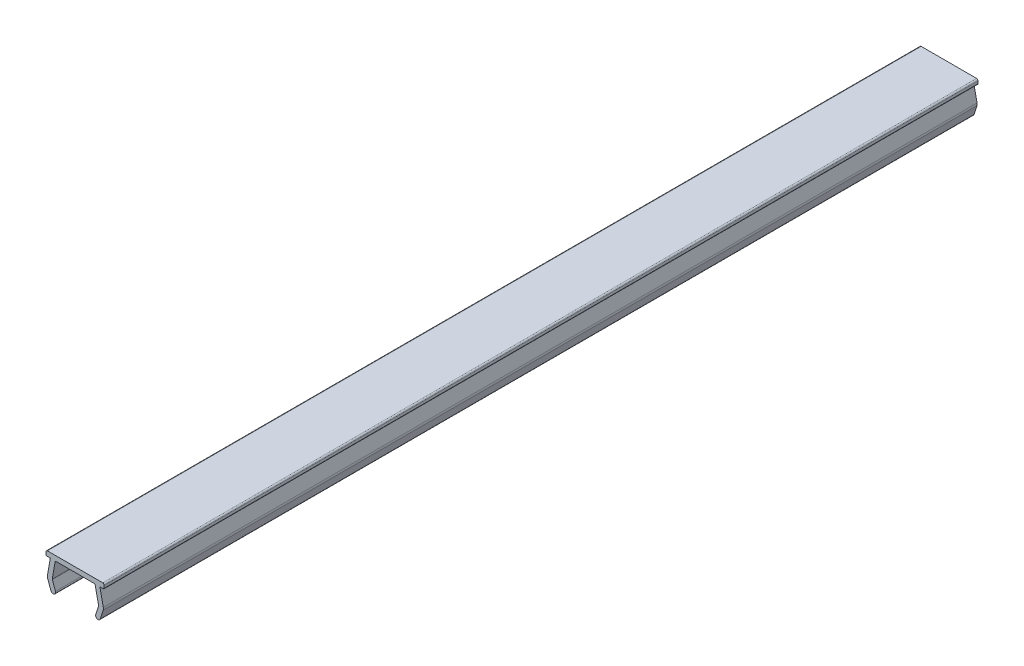
SolidWorks part; units mm, degrees
ref_plane "前视基准面" through (0, 0, 0) normal (0, 0, 1) x (1, 0, 0)
ref_plane "上视基准面" through (0, 0, 0) normal (0, 1, 0) x (1, 0, 0)
ref_plane "右视基准面" through (0, 0, 0) normal (1, 0, 0) x (0, 0, -1)
sketch "草图1" plane through (0, 0, 0) normal (0, 0, 1) x (1, 0, 0)
  line L1 (11.7861, 93.4475) -> (11.1854, 91.5991)
  line L2 (11.107, 97.2884) -> (11.8132, 93.9645)
  line L3 (11.8, 97.2884) -> (11.107, 97.2884)
  line L4 (12, 97.9884) -> (12, 97.4884)
  line L5 (0.3, 98.2884) -> (11.7, 98.2884)
  line L6 (0, 97.4884) -> (0, 97.9884)
  line L7 (0.893, 97.2884) -> (0.2, 97.2884)
  line L8 (0.2946, 93.8947) -> (0.893, 97.2884)
  line L9 (1.0076, 91.5441) -> (0.3398, 93.379)
  line L10 (1.3024, 93.6581) -> (1.9473, 91.8862)
  line L11 (1.8793, 97.1231) -> (1.2911, 93.787)
  line L12 (9.9273, 97.2884) -> (2.0763, 97.2884)
  line L13 (10.8239, 93.8308) -> (10.1229, 97.1299)
  line L14 (10.2343, 91.9082) -> (10.8172, 93.7015)
  arc A0 (11.7861, 93.4475) -> (11.8132, 93.9645) centre (10.8351, 93.7566) ccw
  arc A1 (11.8, 97.2884) -> (12, 97.4884) centre (11.8, 97.4884) ccw
  arc A2 (12, 97.9884) -> (11.7, 98.2884) centre (11.7, 97.9884) ccw
  arc A3 (0.3, 98.2884) -> (0, 97.9884) centre (0.3, 97.9884) ccw
  arc A4 (0, 97.4884) -> (0.2, 97.2884) centre (0.2, 97.4884) ccw
  arc A5 (0.2946, 93.8947) -> (0.3398, 93.379) centre (1.2794, 93.721) ccw
  arc A6 (1.0076, 91.5441) -> (1.9473, 91.8862) centre (1.4774, 91.7151) ccw
  arc A7 (1.2911, 93.787) -> (1.3024, 93.6581) centre (1.5373, 93.7436) ccw
  arc A8 (2.0763, 97.2884) -> (1.8793, 97.1231) centre (2.0763, 97.0884) ccw
  arc A9 (10.1229, 97.1299) -> (9.9273, 97.2884) centre (9.9273, 97.0884) ccw
  arc A10 (10.8172, 93.7015) -> (10.8239, 93.8308) centre (10.5794, 93.7788) ccw
  arc A11 (10.2343, 91.9082) -> (11.1854, 91.5991) centre (10.7098, 91.7537) ccw
extrude "拉伸1" add sketch "草图1" along normal blind 180
move or copy body "Тело-Переместить/Копировать1" [suppressed] bodies to move or copy 101 copy no rotation origin (6, 0, 20) rotation axis (0, 1, 0) rotation angle 90
